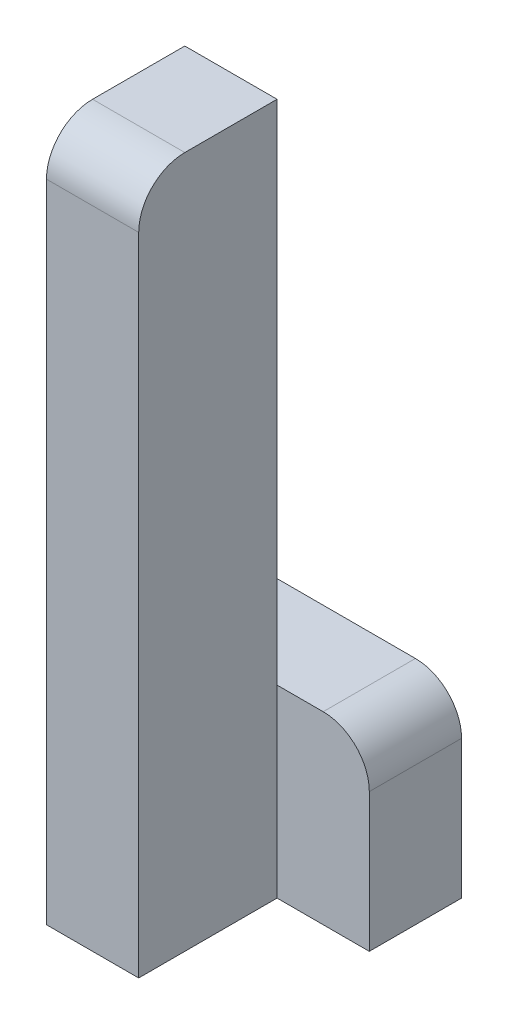
SolidWorks part; units mm, degrees
ref_plane "Front Plane" through (0, 0, 0) normal (0, 0, 1) x (1, 0, 0)
ref_plane "Top Plane" through (0, 0, 0) normal (0, 1, 0) x (1, 0, 0)
ref_plane "Right Plane" through (0, 0, 0) normal (1, 0, 0) x (0, 0, -1)
sketch "Sketch1" plane through (0, 0, 0) normal (0, 0, 1) x (1, 0, 0)
  line L1 (-30, -150) -> (-10, -150)
  line L2 (-10, -150) -> (-10, 0)
  line L3 (-10, 0) -> (-30, 0)
  line L4 (-30, 0) -> (-30, -150)
  dimension "D1" = 20
  dimension "Width" = 150
extrude "Boss-Extrude1" add sketch "Sketch1" along normal blind 30
sketch "Sketch2" plane through (0, 0, 0) normal (0, 0, 1) x (1, 0, 0)
  line L1 (-30, -150) -> (10, -150)
  line L2 (10, -150) -> (10, -110)
  line L3 (10, -110) -> (-30, -110)
  line L4 (-30, -110) -> (-30, -150)
  dimension "D1" = 40
  dimension "Width" = 40
extrude "Boss-Extrude2" add sketch "Sketch2" against normal blind 20
fillet "Fillet1" radius 10 2 edges at (10, -110, -10) (-20, 0, 30)
